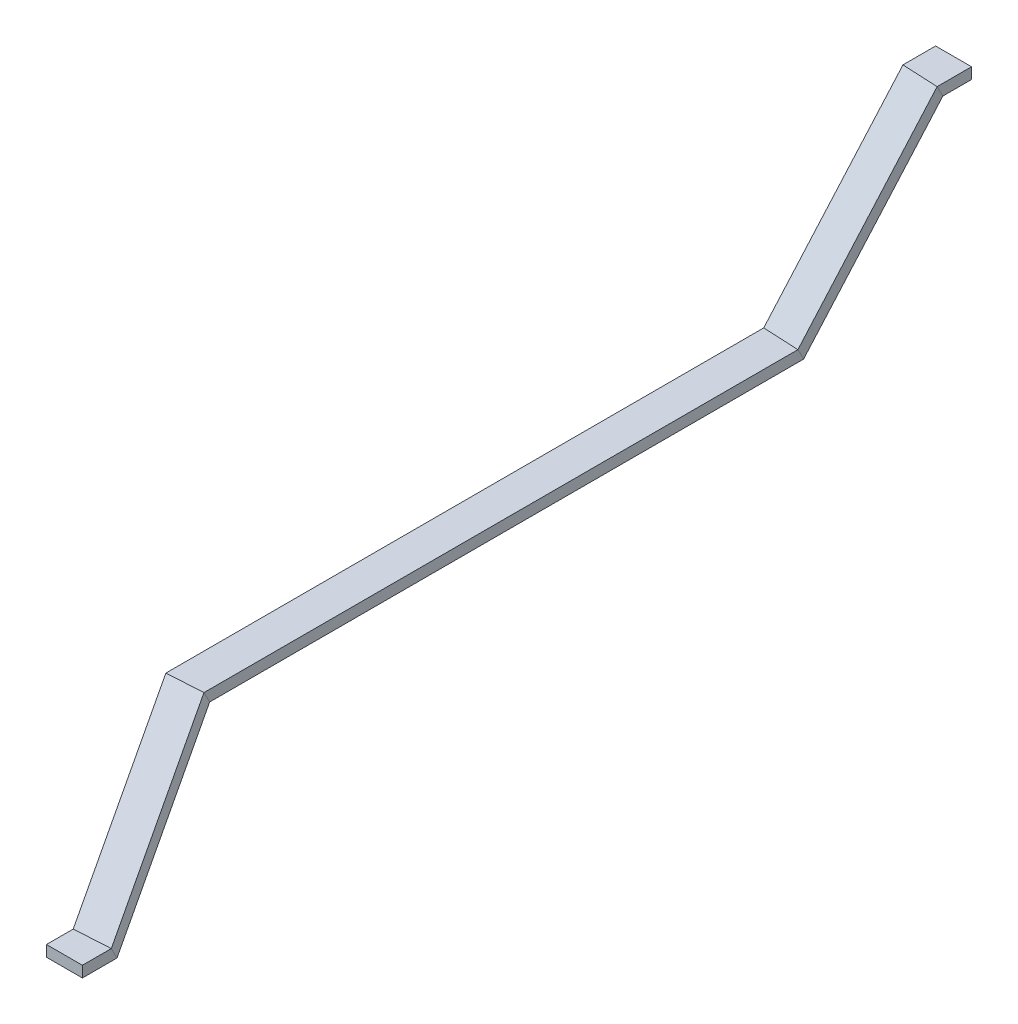
SolidWorks part; units mm, degrees
ref_plane "Front Plane" through (0, 0, 0) normal (0, 0, 1) x (1, 0, 0)
ref_plane "Top Plane" through (0, 0, 0) normal (0, 1, 0) x (1, 0, 0)
ref_plane "Right Plane" through (0, 0, 0) normal (1, 0, 0) x (0, 0, -1)
sketch3d "3DSketch1"
  line L0 (3251.1818, -307.3272, 1441.6243) -> (3251.1818, -307.3272, 1381.6243)
  line L1 (3215.675, 0, 1165) -> (3251.1818, -307.3272, 1381.6243)
  line L2 (3215.675, 0, 0) -> (3247.7853, 341.356, -240.0752)
  line L3 (3215.675, 0, 1165) -> (3215.675, 0, 0)
  line L6 (3247.7853, 341.356, -240.0752) -> (3247.7853, 341.356, -300.0752)
  point P0 (3215.675, 0, 0)
  point P1 (0, 0, 0)
  point P2 (3247.7853, 341.356, -300.0752)
  point P3 (3215.675, 0, 1165)
  point P7 (0, 0, 0)
  point P12 (3251.1818, -307.3272, 1381.6243)
  point P15 (3247.7853, 341.356, -240.0752)
  point P21 (3251.1818, -307.3272, 1441.6243)
  dimension "D1" = 1165
  dimension "D5" = 3251.1818
  dimension "D6" = 307.3272
  dimension "D8" = 60
  dimension "D12" = 3247.7853
  dimension "D13" = 341.356
  dimension "D15" = 60
  dimension "D2" = 125
  dimension "D3" = 125
ref_plane "Plane2" through (3247.7853, 341.356, -300.0752) normal (0, 0, 1) x (1, 0, 0)
sketch "Sketch2" plane through (3247.7853, 341.356, -300.0752) normal (0, 0, 1) x (1, 0, 0)
  line L1 (-35.125, 10.8) -> (35.125, 10.8)
  line L2 (-35.125, 10.8) -> (-35.125, -10.8)
  line L3 (-35.125, -10.8) -> (35.125, -10.8)
  line L4 (35.125, 10.8) -> (35.125, -10.8)
  point P4 (35.125, 0)
  point P5 (0, 10.8)
  dimension "D1" = 21.6
  dimension "D2" = 70.25
sweep "Sweep1" add profiles "Sketch2" path "3DSketch1"
equation "\"axialLength\"= 925mm"
equation "\"lengthAfterAxial\"= 240mm"
equation "\"Di\"= 6197.6mm'stator inner diameter"
equation "\"wedgeHeight\"= 4mm"
equation "\"spacerHeight\"= 7.5mm"
equation "\"coilHeight\"= 70.25mm'with isolation"
equation "\"coilWidth\"= 21.6mm'with isolation"
equation "\"r1\"= \"Di\" / 2 + \"wedgeHeight\" + \"spacerHeight\" + \"coilHeight\" * 3 / 2 + 50mm"
equation "\"theta1\"= 1deg"
equation "\"z1\"= \"axialLength\" + \"lengthAfterAxial\" + 50mm"
equation "\"D1@3DSketch1\"= \"axialLength\" + \"lengthAfterAxial\""
equation "\"r2\"= \"r1\""
equation "\"theta2\"= 4.5 * 1.2deg"
equation "\"z2\"= \"z1\" + 200mm"
equation "\"D5@3DSketch1\"= \"r2\" * cos ( \"theta2\" )"
equation "\"D6@3DSketch1\"= \"r2\" * sin ( \"theta2\" )"
equation "\"connectionHeight\"= 120mm'height of the joint part"
equation "\"r3\"= \"r1\""
equation "\"theta3\"= 1deg"
equation "\"z3\"= 50mm"
equation "\"r4\"= \"r3\""
equation "\"theta4\"= 1.2 * 5deg"
equation "\"z4\"= \"z3\" + 200mm"
equation "\"D12@3DSketch1\"= \"r4\" * cos ( \"theta4\" )"
equation "\"D13@3DSketch1\"= \"r4\" * sin ( \"theta4\" )"
equation "\"D15@3DSketch1\"= \"connectionHeight\" / 2"
equation "\"fillet\"= 30mm"
equation "\"D1@Sketch2\"= \"coilWidth\""
equation "\"D2@Sketch2\"= \"coilHeight\""
equation "\"endWindingAngle\"= 125deg"
equation "\"D2@3DSketch1\"= \"endWindingAngle\""
equation "\"D3@3DSketch1\"= \"endWindingAngle\""
